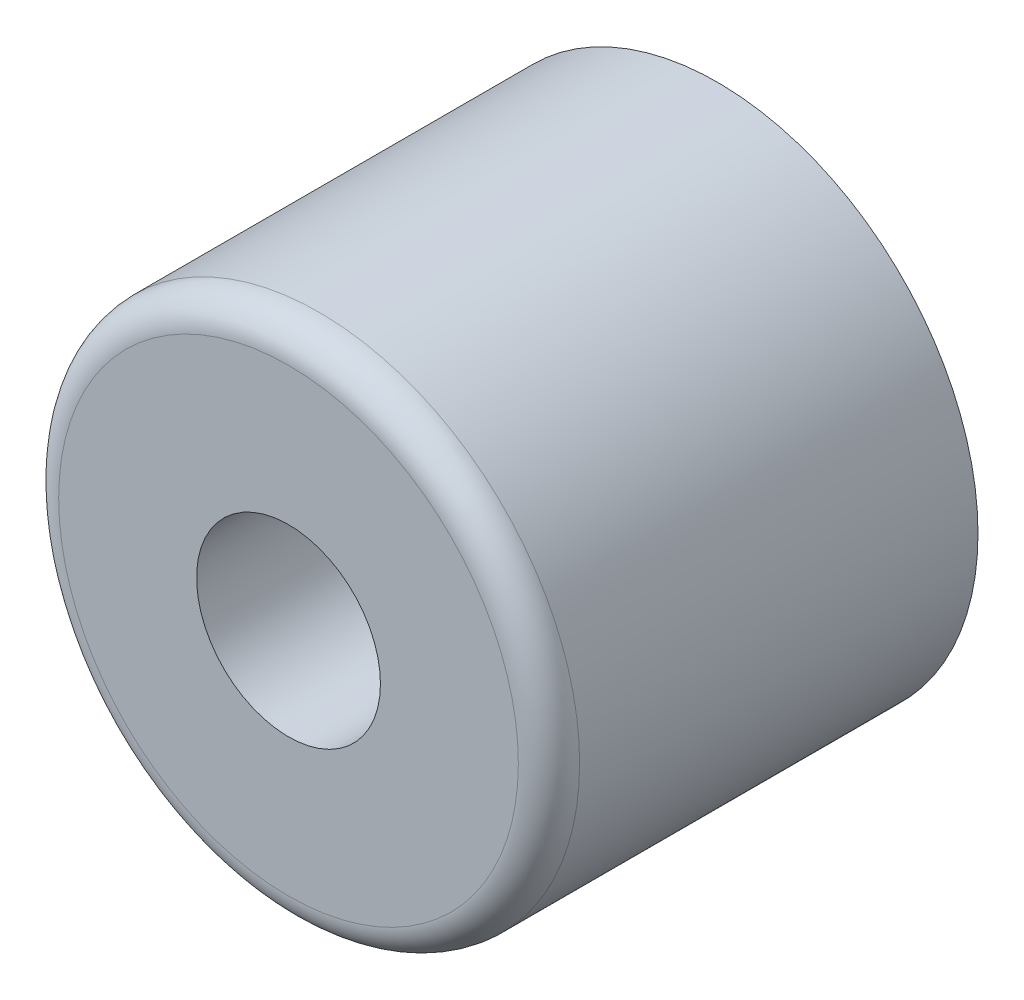
SolidWorks part; units mm, degrees
ref_plane "Front" through (0, 0, 0) normal (0, 0, 1) x (1, 0, 0)
ref_plane "Top" through (0, 0, 0) normal (0, 1, 0) x (1, 0, 0)
ref_plane "Right" through (0, 0, 0) normal (1, 0, 0) x (0, 0, -1)
sketch "Sketch1" plane through (0, 0, 0) normal (0, 0, 1) x (1, 0, 0)
  circle A0 centre (0, 0) radius 42.5
  circle A1 centre (0, 0) radius 15
  dimension "D1" = 85
  dimension "D2" = 30
extrude "Boss-Extrude1" add sketch "Sketch1" along normal blind 70
fillet "Fillet1" radius 5 1 edges at (42.5, 0, 70)
